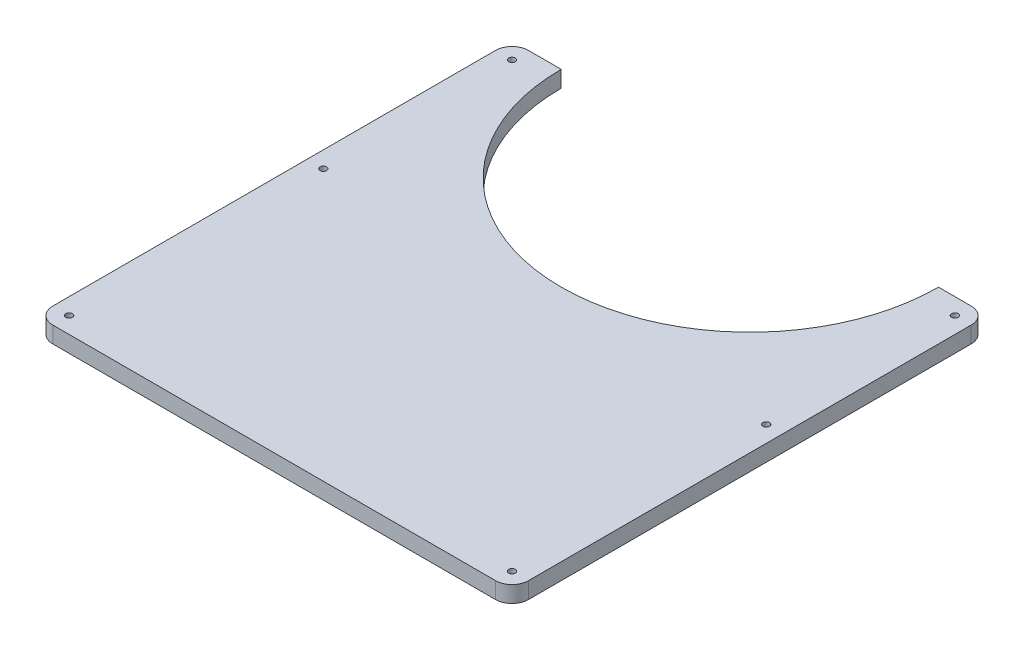
SolidWorks part; units mm, degrees
material "Acrylique (impact moyen-haut)"
ref_plane "Plan de face" through (0, 0, 0) normal (0, 0, 1) x (1, 0, 0)
ref_plane "Plan de dessus" through (0, 0, 0) normal (0, 1, 0) x (1, 0, 0)
ref_plane "Plan de droite" through (0, 0, 0) normal (1, 0, 0) x (0, 0, -1)
sketch "Esquisse2" plane through (0, 0, 0) normal (0, 1, 0) x (1, 0, 0)
  line L0 (145, 290) -> (145, 0) construction
  line L1 (0, 0) -> (290, 0)
  line L2 (0, 0) -> (0, 290)
  line L3 (0, 290) -> (30, 290)
  line L4 (290, 0) -> (290, 290)
  line L5 (0, 145) -> (290, 145) construction
  line L6 (290, 290) -> (260, 290)
  arc A0 (30, 290) -> (260, 290) centre (145, 290) ccw
  dimension "D1" = 290
  dimension "D2" = 290
  dimension "D3" = 30
extrude "Boss.-Extru.1" add sketch "Esquisse2" along normal blind 10
sketch "Esquisse3" plane through (0, 10, 0) normal (0, 1, 0) x (1, 0, 0)
  line L0 (0, 145) -> (290, 145) construction
  line L1 (0, 290) -> (0, 0) construction
  line L2 (290, 0) -> (290, 290) construction
  line L3 (145, 290) -> (145, 0) construction
  line L5 (0, 0) -> (290, 0) construction
  line L6 (0, 290) -> (0, 0) construction
  line L8 (30, 290) -> (0, 290) construction
  circle A0 centre (10, 280) radius 2
  circle A1 centre (280, 280) radius 2
  circle A2 centre (280, 10) radius 2
  circle A3 centre (10, 10) radius 2
  dimension "D3" = 4
  dimension "D1" = 10
  dimension "D2" = 10
extrude "Enlèv. mat.-Extru.1" cut sketch "Esquisse3" against normal blind 10
fillet "Congé1" radius 10 4 edges at (0, 5, 0) (290, 5, 0) (290, 5, -290) (0, 5, -290)
sketch "Esquisse4" plane through (0, 10, 0) normal (0, 1, 0) x (1, 0, 0)
  circle A0 centre (10, 165) radius 2
  circle A1 centre (280, 165) radius 2
extrude "Enlèv. mat.-Extru.2" cut sketch "Esquisse4" against normal blind 10
sketch "Esquisse6" plane through (0, 0, 0) normal (0, -1, 0) x (1, 0, 0)
  circle A0 centre (10, -10) radius 6
  circle A1 centre (280, -10) radius 6
  circle A2 centre (280, -165) radius 6
  circle A3 centre (280, -280) radius 6
  circle A4 centre (10, -280) radius 6
  circle A5 centre (10, -165) radius 6
  dimension "D1" = 12
extrude "Enlèv. mat.-Extru.4" cut sketch "Esquisse6" against normal blind 5
